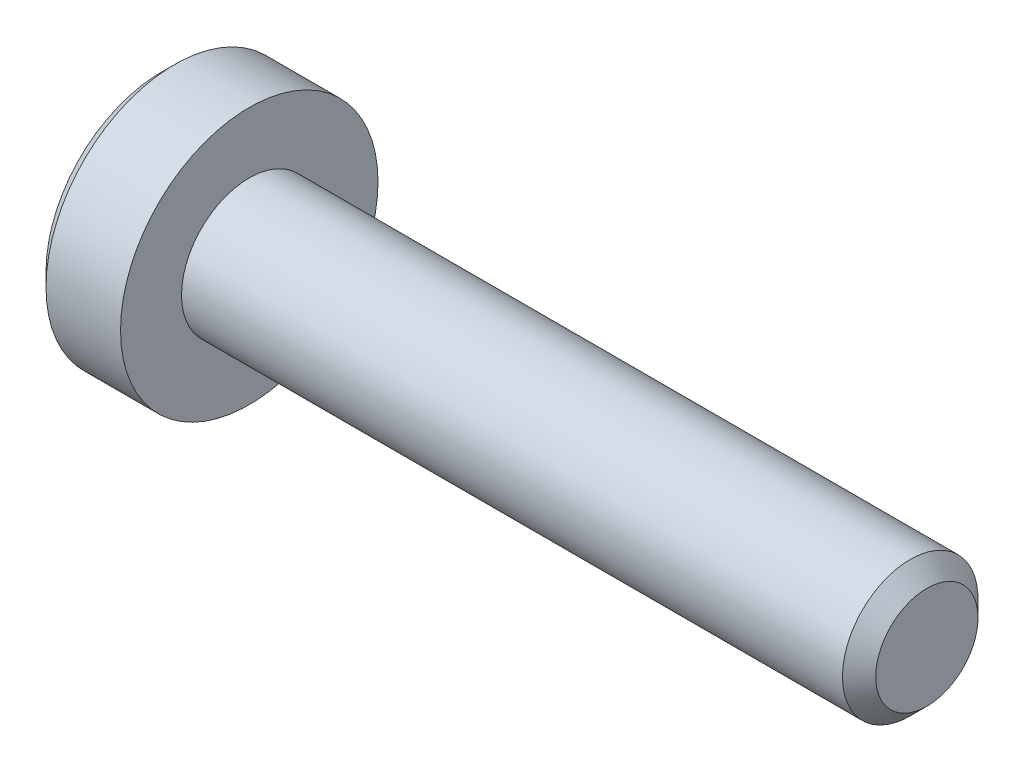
SolidWorks part; units mm, degrees
material "AISI 304"
ref_plane "正面" through (0, 0, 0) normal (0, 0, 1) x (1, 0, 0)
ref_plane "平面" through (0, 0, 0) normal (0, 1, 0) x (1, 0, 0)
ref_plane "右側面" through (0, 0, 0) normal (1, 0, 0) x (0, 0, -1)
ref_plane "Plane1" through (0, 0, 0) normal (0, 0, 1) x (1, 0, 0)
sketch "Sketch1" plane through (0, 0, 0) normal (0, 0, 1) x (1, 0, 0)
  line L0 (-1.3, 0) -> (-1.3, 1.7)
  line L1 (-1.3, 1.7) -> (-1.1, 1.9)
  line L2 (-1.1, 1.9) -> (0, 1.9)
  line L3 (0, 1.9) -> (0, 1)
  line L4 (0, 1) -> (9.7545, 1)
  line L5 (9.7545, 1) -> (10, 0.7545)
  line L6 (10, 0.7545) -> (10, 0)
  line L7 (10, 0) -> (-1.3, 0)
  line L8 (10, 0) -> (-1.3, 0) construction
revolve "Revolve1" add sketch "Sketch1" angle 360 about L8
cosmetic thread "Cosmetic Thread1" parameters "D1"=9.5748, "D2"=1.509
ref_plane "Plane2" through (-1.3, 0, 0) normal (1, 0, 0) x (0, 0, -1)
sketch "Sketch2" plane through (-1.3, 0, 0) normal (1, 0, 0) x (0, 0, -1)
  line L0 (-0.65, -0.3753) -> (0, -0.7506)
  line L1 (0, -0.7506) -> (0.65, -0.3753)
  line L2 (0.65, -0.3753) -> (0.65, 0.3753)
  line L3 (0.65, 0.3753) -> (0, 0.7506)
  line L4 (0, 0.7506) -> (-0.65, 0.3753)
  line L5 (-0.65, 0.3753) -> (-0.65, -0.3753)
extrude "Cut-Extrude1" cut sketch "Sketch2" along normal blind 0.7
